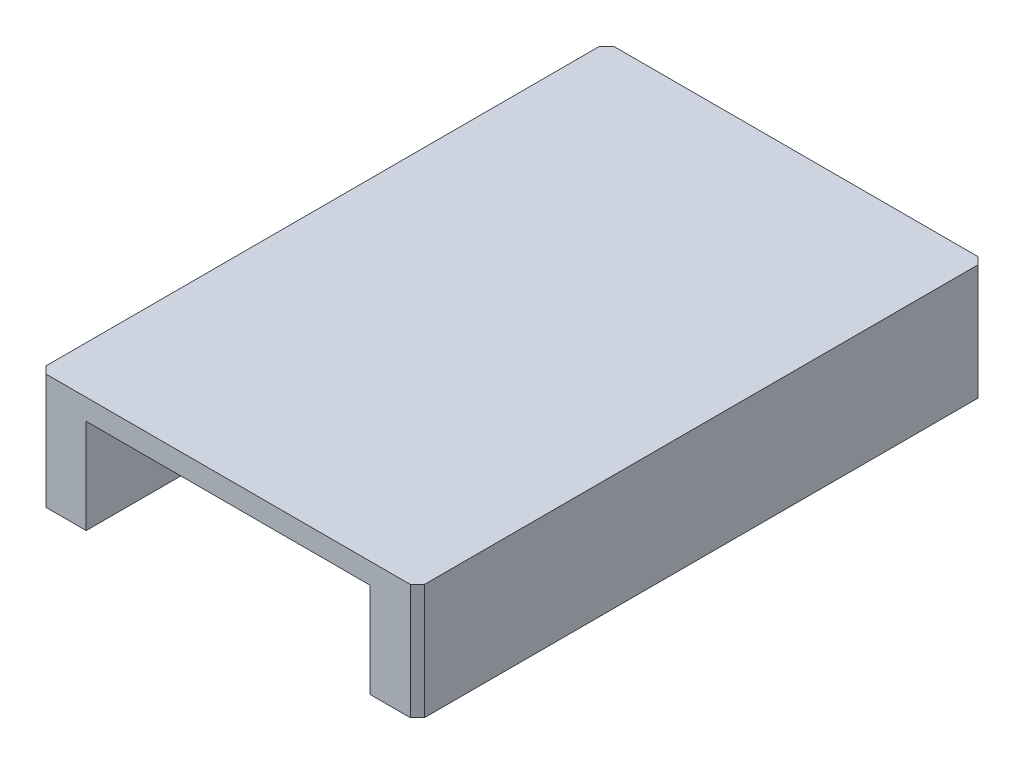
SolidWorks part; units mm, degrees
material "PLA"
ref_plane "Piano frontale" through (0, 0, 0) normal (0, 0, 1) x (1, 0, 0)
ref_plane "Piano superiore" through (0, 0, 0) normal (0, 1, 0) x (1, 0, 0)
ref_plane "Piano destro" through (0, 0, 0) normal (1, 0, 0) x (0, 0, -1)
sketch "Schizzo1" plane through (0, 0, 0) normal (1, 0, 0) x (0, 0, -1)
  line L0 (0, 0) -> (0, 7.2)
  line L1 (0, 7.2) -> (60, 7.2)
  line L2 (60, 7.2) -> (60, 0)
  line L3 (60, 0) -> (0, 0)
  line L8 (33.625, 6.1) -> (33.625, 1.1)
  line L9 (33.625, 1.1) -> (52.75, 1.1)
  line L10 (52.75, 1.1) -> (52.75, 6.1)
  line L11 (52.75, 6.1) -> (33.625, 6.1)
  line L12 (30, 7.2) -> (30, 0) construction
  line L13 (7.25, 1.1) -> (7.25, 6.1)
  line L14 (26.375, 1.1) -> (7.25, 1.1)
  line L15 (26.375, 6.1) -> (26.375, 1.1)
  line L16 (7.25, 6.1) -> (26.375, 6.1)
  dimension "D1" = 7.2
  dimension "D2" = 7.25
  dimension "D3" = 5
  dimension "D4" = 7.25
  dimension "D5" = 60
  dimension "D6" = 1.1
extrude "Estrusione-Estrusione1" add sketch "Schizzo1" along normal blind 40
sketch "Schizzo2" plane through (0, 0, 0) normal (0, 0, 1) x (1, 0, 0)
  line L0 (5, 0) -> (5, 5)
  line L1 (40, 0) -> (0, 0) construction
  line L2 (5, 5) -> (16.375, 5)
  line L3 (16.375, 5) -> (16.375, 0)
  line L4 (16.375, 0) -> (5, 0)
  line L5 (20, 7.2) -> (20, 0) construction
  line L6 (40, 7.2) -> (0, 7.2) construction
  line L8 (0, 7.2) -> (0, 0) construction
  line L9 (23.625, 5) -> (23.625, 0)
  line L14 (14.3, 7.2) -> (16.375, 7.2)
  line L15 (14.3, 7.2) -> (14.3, 6.1)
  line L16 (14.3, 6.1) -> (16.375, 6.1)
  line L17 (16.375, 7.2) -> (16.375, 6.1)
  line L18 (7.25, 7.2) -> (9.3, 7.2)
  line L19 (7.25, 7.2) -> (7.25, 6.1)
  line L20 (7.25, 6.1) -> (9.3, 6.1)
  line L21 (9.3, 7.2) -> (9.3, 6.1)
  line L22 (35, 5) -> (23.625, 5)
  line L23 (35, 0) -> (35, 5)
  line L24 (23.625, 0) -> (35, 0)
  line L25 (25.7, 6.1) -> (23.625, 6.1)
  line L26 (23.625, 7.2) -> (23.625, 6.1)
  line L27 (25.7, 7.2) -> (23.625, 7.2)
  line L28 (25.7, 7.2) -> (25.7, 6.1)
  line L29 (32.75, 6.1) -> (30.7, 6.1)
  line L30 (30.7, 7.2) -> (30.7, 6.1)
  line L31 (32.75, 7.2) -> (30.7, 7.2)
  line L32 (32.75, 7.2) -> (32.75, 6.1)
  dimension "D1" = 5
  dimension "D2" = 3.625
  dimension "D3" = 2.2
  dimension "D4" = 1.1
  dimension "D5" = 7.25
  dimension "D6" = 3.625
  dimension "D7" = 21.4
  dimension "D8" = 1.1
  dimension "D9" = 5
extrude "Taglio-Estrusione1" cut sketch "Schizzo2" against normal through all
chamfer "Smusso1" distance 0.75 angle 45 4 edges at (0, 3.6, -60) (40, 3.6, -60) (40, 3.6, 0) (0, 3.6, 0)
sketch "Schizzo3" plane through (0, 0, 0) normal (0, 0, 1) x (1, 0, 0)
  line L1 (16.375, 0) -> (23.625, 0)
  line L2 (16.375, 0) -> (16.375, 5)
  line L3 (16.375, 5) -> (23.625, 5)
  line L4 (23.625, 0) -> (23.625, 5)
extrude "Taglio-Estrusione2" cut sketch "Schizzo3" against normal blind 64
sketch "Schizzo4" plane through (0, 0, 0) normal (0, 0, 1) x (1, 0, 0)
  line L6 (39.25, 0) -> (39.25, 7.2) construction
  line L7 (0.75, 7.2) -> (39.25, 7.2)
  line L8 (0.75, 7.2) -> (0.75, 6.1)
  line L9 (0.75, 6.1) -> (39.25, 6.1)
  line L10 (39.25, 7.2) -> (39.25, 6.1)
  dimension "D1" = 1.1
extrude "Estrusione-Estrusione3" add sketch "Schizzo4" against normal blind 60
sketch "Schizzo7" plane through (0, 0, -52.75) normal (0, 0, 1) x (1, 0, 0)
  line L0 (40, 6.1) -> (0, 6.1) construction
  line L1 (35, 5) -> (5, 5)
  line L2 (35, 5) -> (35, 6.1)
  line L3 (35, 6.1) -> (5, 6.1)
  line L4 (5, 5) -> (5, 6.1)
extrude "Estrusione-Estrusione4" add sketch "Schizzo7" along normal blind 50
sketch "Schizzo8" plane through (0, 0, 0) normal (0, -1, 0) x (1, 0, 0)
  line L0 (5, 0) -> (0.75, 0)
  line L1 (0.75, 0) -> (0, -0.75)
  line L2 (0, -0.75) -> (0, -59.25)
  line L3 (0, -59.25) -> (0.75, -60)
  line L4 (0.75, -60) -> (5, -60)
  line L5 (5, -60) -> (5, 0)
  line L6 (35, 0) -> (35, -60)
  line L7 (35, -60) -> (39.25, -60)
  line L8 (39.25, -60) -> (40, -59.25)
  line L9 (40, -59.25) -> (40, -0.75)
  line L10 (40, -0.75) -> (39.25, 0)
  line L11 (39.25, 0) -> (35, 0)
extrude "Estrusione-Estrusione5" add sketch "Schizzo8" along normal blind 5
sketch "Schizzo9" plane through (35, 0, 0) normal (1, 0, 0) x (0, 0, -1)
  line L1 (7.25, 6.1) -> (26.375, 6.1)
  line L2 (7.25, 6.1) -> (7.25, 5)
  line L3 (7.25, 5) -> (26.375, 5)
  line L4 (26.375, 6.1) -> (26.375, 5)
  line L5 (33.625, 6.1) -> (52.75, 6.1)
  line L6 (33.625, 6.1) -> (33.625, 5)
  line L7 (33.625, 5) -> (52.75, 5)
  line L8 (52.75, 6.1) -> (52.75, 5)
extrude "Estrusione-Estrusione6" add sketch "Schizzo9" along normal blind 5 and the other way blind 35
sketch "Schizzo10" plane through (0, 0, 0) normal (-1, 0, 0) x (0, 0, 1)
  line L1 (-52.75, 1.1) -> (-33.625, 1.1)
  line L2 (-52.75, 1.1) -> (-52.75, -2.8)
  line L3 (-52.75, -2.8) -> (-33.625, -2.8)
  line L4 (-33.625, 1.1) -> (-33.625, -2.8)
  line L5 (-26.375, 1.1) -> (-7.25, 1.1)
  line L6 (-26.375, 1.1) -> (-26.375, -2.8)
  line L7 (-26.375, -2.8) -> (-7.25, -2.8)
  line L8 (-7.25, 1.1) -> (-7.25, -2.8)
  line L10 (-33.625, 5) -> (-52.75, 5) construction
  line L11 (-7.25, 5) -> (-26.375, 5) construction
  dimension "D1" = 3.9
extrude "Taglio-Estrusione3" cut sketch "Schizzo10" against normal through all
sketch "Schizzo11" plane through (0, 0, 0) normal (-1, 0, 0) x (0, 0, 1)
  line L1 (-52.75, -2.8) -> (-33.625, -2.8)
  line L2 (-52.75, -2.8) -> (-52.75, 5)
  line L3 (-52.75, 5) -> (-33.625, 5)
  line L4 (-33.625, -2.8) -> (-33.625, 5)
  line L5 (-26.375, -2.8) -> (-7.25, -2.8)
  line L6 (-26.375, -2.8) -> (-26.375, 5)
  line L7 (-26.375, 5) -> (-7.25, 5)
  line L8 (-7.25, -2.8) -> (-7.25, 5)
extrude "Estrusione-Estrusione7" add sketch "Schizzo11" against normal blind 40
sketch "Schizzo12" plane through (0, 0, -60) normal (0, 0, -1) x (-1, 0, 0)
  line L1 (-35, -5) -> (-5, -5)
  line L2 (-35, -5) -> (-35, 5)
  line L3 (-35, 5) -> (-5, 5)
  line L4 (-5, -5) -> (-5, 5)
extrude "Taglio-Estrusione4" cut sketch "Schizzo12" against normal blind 64
